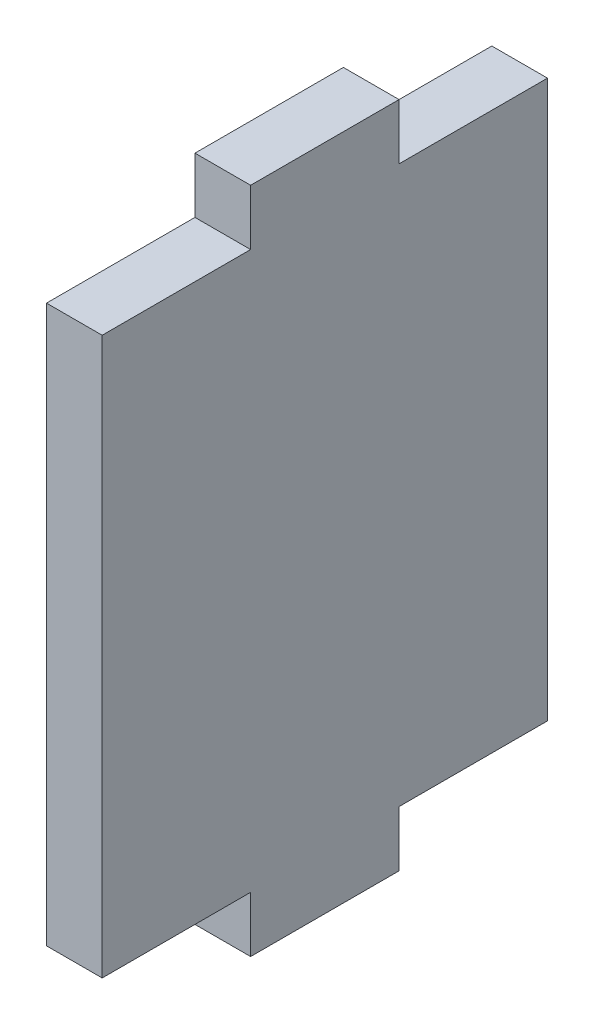
SolidWorks part; units mm, degrees
ref_plane "Ön Düzlem" through (0, 0, 0) normal (0, 0, 1) x (1, 0, 0)
ref_plane "Üst Düzlem" through (0, 0, 0) normal (0, 1, 0) x (1, 0, 0)
ref_plane "Sağ Düzlem" through (0, 0, 0) normal (1, 0, 0) x (0, 0, -1)
sketch "Sketch1" plane through (0, 0, 0) normal (1, 0, 0) x (0, 0, -1)
  line L0 (4, 15) -> (12, 15)
  line L1 (4, -18) -> (-4, -18)
  line L2 (12, -15) -> (12, 15)
  line L3 (4, 18) -> (-4, 18)
  line L4 (-12, -15) -> (-12, 15)
  line L5 (10, -15) -> (-10, 15) construction
  line L6 (10, 15) -> (-10, -15) construction
  line L7 (-4, -18) -> (4, -18)
  line L8 (-4, -18) -> (-4, -15)
  line L10 (4, -15) -> (4, -18)
  line L11 (4, -15) -> (12, -15)
  line L12 (-4, -15) -> (-12, -15)
  line L14 (4, 15) -> (4, 18)
  line L15 (4, 18) -> (-4, 18)
  line L16 (-4, 18) -> (-4, 15)
  line L17 (-4, 15) -> (-12, 15)
  point P0 (0, 0)
extrude "Boss-Extrude1" add sketch "Sketch1" along normal blind 3 contours L16 L17 L4 L12 L8 L1 L10 L11 L2 L0 L14 L3
